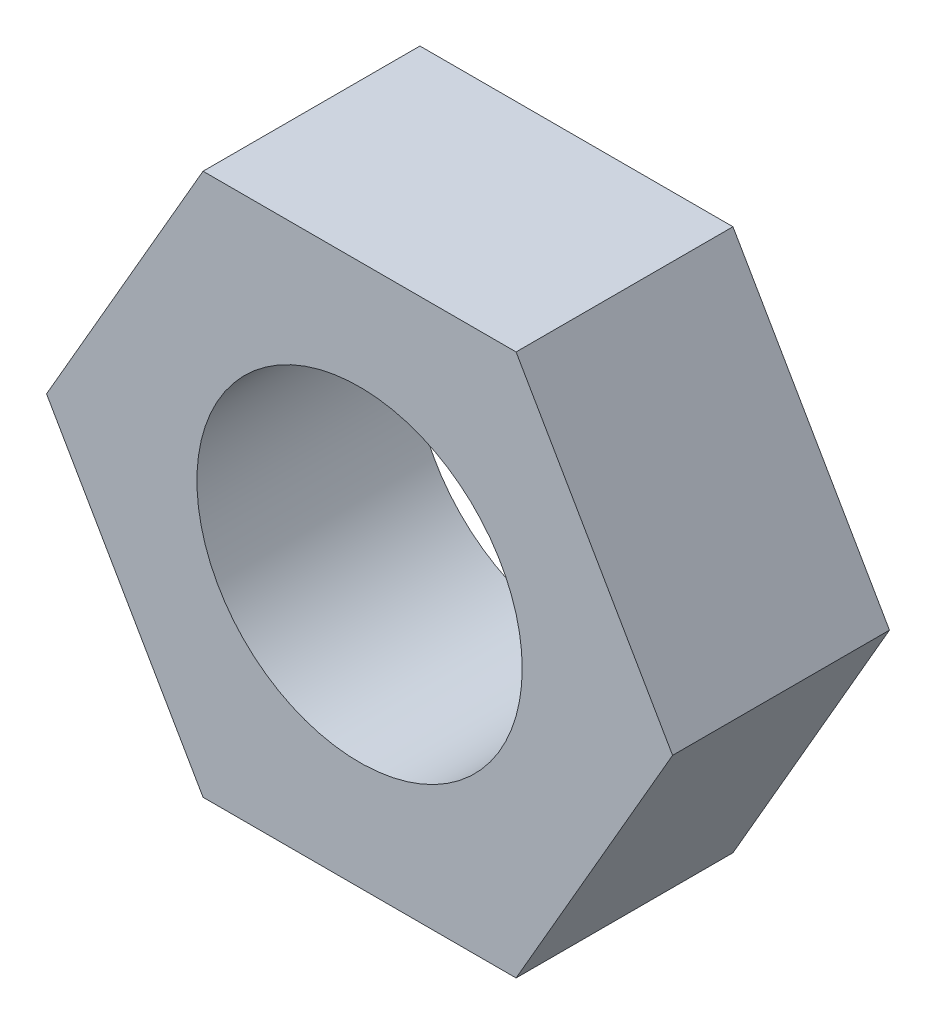
SolidWorks part; units mm, degrees
material "AISI 1018"
ref_plane "Front Plane" through (0, 0, 0) normal (0, 0, 1) x (1, 0, 0)
ref_plane "Top Plane" through (0, 0, 0) normal (0, 1, 0) x (1, 0, 0)
ref_plane "Right Plane" through (0, 0, 0) normal (1, 0, 0) x (0, 0, -1)
ref_plane "Plane1"
sketch "Sketch1" plane through (0, 0, 0) normal (0, 0, 1) x (1, 0, 0)
  line L0 (5.7735, 0) -> (2.8868, 5)
  line L1 (2.8868, 5) -> (-2.8868, 5)
  line L2 (-2.8868, 5) -> (-5.7735, 0)
  line L3 (-5.7735, 0) -> (-2.8868, -5)
  line L4 (-2.8868, -5) -> (2.8868, -5)
  line L5 (2.8868, -5) -> (5.7735, 0)
extrude "Extrusion1" add sketch "Sketch1" against normal blind 4
sketch "Sketch2" plane through (0, 0, 0) normal (0, 0, 1) x (1, 0, 0)
  circle A0 centre (0, 0) radius 3
  dimension "D1" = 6
extrude "Thread1" cut sketch "Sketch2" against normal blind 4
